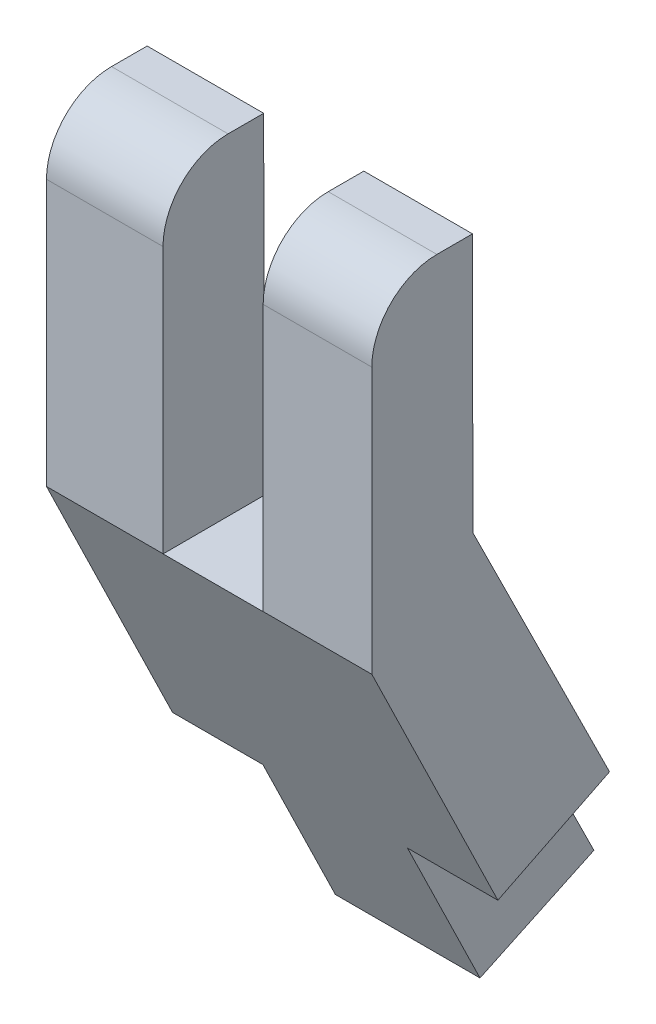
SolidWorks part; units mm, degrees
ref_plane "Front Plane" through (0, 0, 0) normal (0, 0, 1) x (1, 0, 0)
ref_plane "Top Plane" through (0, 0, 0) normal (0, 1, 0) x (1, 0, 0)
ref_plane "Right Plane" through (0, 0, 0) normal (1, 0, 0) x (0, 0, -1)
sketch "Sketch1" plane through (0, 0, 0) normal (0, 0, 1) x (1, 0, 0)
  line L0 (-2.5151, 0) -> (7.5105, 0) construction
  line L1 (2.4977, 0) -> (2.4977, 5.0158) construction
  line L3 (2.4977, 4.6362) -> (2.4977, 5.0158)
  line L5 (-2.8151, 0.4082) -> (-2.4998, 0.4072)
  line L6 (-2.5151, -0.4082) -> (-2.8151, -0.4082)
  arc A2 (-2.8151, 0.4082) -> (-2.8151, -0.4082) centre (-2.8151, 0) ccw
  arc A5 (-2.1151, 0.0013) -> (-2.5151, -0.4082) centre (-2.5234, 0) cw
  arc A6 (-2.1151, 0.0013) -> (2.4977, 4.6362) centre (2.5819, -0.0604) cw
  arc A7 (-2.4998, 0.4072) -> (2.4977, 5.0158) centre (2.4848, 0.0158) cw
revolve "Revolve1" [suppressed] add sketch "Sketch1" angle 360 about L1
sketch "Sketch3" plane through (0, 0, 0) normal (1, 0, 0) x (0, 0, -1)
  line L0 (-5.1915, 13.2582) -> (-5.1862, 9.6741)
  line L1 (-2.2625, 3.7845) -> (-3.8381, 3.0429)
  line L6 (-6.5841, 8.6789) -> (-6.5841, 13.2582)
  line L7 (-6.5841, 13.2582) -> (-5.1915, 13.2582)
  line L12 (-2.2625, 3.7845) -> (-5.1862, 9.6741)
  line L13 (-3.8381, 3.0429) -> (-6.5841, 8.6789)
extrude "Boss-Extrude1" add sketch "Sketch3" along normal blind 4.5 separate body
sketch "Sketch4" plane through (0, -0.0108, 5.1659) normal (0, 0.0021, -1) x (-1, 0, 0)
  line L0 (-2.997, 8.6897) -> (-2.997, 13.2897)
  line L1 (-2.997, 8.6897) -> (-1.6118, 8.6897)
  line L2 (-1.6118, 8.6897) -> (-1.6118, 13.2897)
  line L3 (-2.997, 13.2897) -> (-1.6118, 13.2897)
extrude "Cut-Extrude1" cut sketch "Sketch4" against normal up to next and the other way blind 4.5
sketch "Sketch5" plane through (0, 0, 0) normal (0, 0, 1) x (1, 0, 0)
  line L0 (-0.8483, 3.3998) -> (-0.8483, 3.73)
  line L1 (-4.3349, 3.3998) -> (-4.5715, 3.5649)
  line L2 (-4.0983, 3.3998) -> (-4.3349, 3.3998)
  line L3 (-4.5715, 3.5649) -> (-4.5715, 3.73)
  line L4 (-4.5715, 3.73) -> (-0.8483, 3.73)
  line L5 (-2.7483, 3.3998) -> (-0.8483, 3.3998)
  line L6 (-2.7483, 3.3998) -> (-2.7483, 2.9514)
  line L7 (-2.7483, 2.9514) -> (-4.0983, 3.3998)
  line L9 (-2.1455, 4.33) -> (-4.3035, 4.33) construction
revolve "Revolve2" [suppressed] add sketch "Sketch5" angle 360 about L9
sketch "Sketch6" [suppressed] plane through (-3.9715, 0, 0) normal (-1, 0, 0) x (0, 0, 1)
  circle A0 centre (0, 4.33) radius 0.6
extrude "Cut-Extrude2" [suppressed] cut sketch "Sketch6" against normal blind 6
sketch "Sketch7" [suppressed] plane through (-0.8483, 0, 0) normal (1, 0, 0) x (0, 0, -1)
  arc A2 (0.668, 3.6826) -> (-0.668, 3.6826) centre (0, 4.33) ccw construction
  circle A4 centre (0, 4.33) radius 0.9302
  circle A5 centre (0, 4.33) radius 0.6
extrude "Boss-Extrude2" [suppressed] add sketch "Sketch7" along normal blind 4
sketch "Sketch8" [suppressed] plane through (0, 0, 0) normal (0, 0, 1) x (1, 0, 0)
  line L0 (7.1105, 0.0013) -> (2.4977, 0.0013)
  line L1 (7.1105, 0.0013) -> (-2.1151, 0.0013) construction
  line L2 (2.4977, 0.0013) -> (2.4977, 4.5956)
  arc A0 (7.1105, 0.0013) -> (2.4977, 4.5956) centre (2.5366, 0.0217) ccw
  spline S0 degree 3 poles (3.1517, 4.5407) (2.9658, 4.5712) (2.7792, 4.5898) (2.404, 4.5991) (2.2144, 4.5893) (2.0285, 4.567) knots 0 0 0 0 0.5 0.5 1 1 1 1 construction
revolve "Cut-Revolve1" [suppressed] cut sketch "Sketch8" angle 360 about L2
fillet "Fillet1" radius 0.9 2 edges at (0.8059, 13.2582, 6.5841) (3.7485, 13.2582, 6.5841)
sketch "Sketch9" plane through (0, -0.1529, 0.308) normal (0, 0.4446, -0.8957) x (-1, 0, 0)
  line L0 (-2.25, 4.3959) -> (-2.25, 7.3959) construction
  line L1 (-4.5, 4.3959) -> (0, 4.3959) construction
  line L2 (0, 6.7208) -> (0, 4.3959)
  line L3 (-1.25, 6.7208) -> (-1.25, 4.3959)
  line L4 (-3.25, 6.7208) -> (-3.25, 4.3959)
  line L5 (0, 4.3959) -> (0, 10.9711) construction
  line L6 (-4.5, 6.7208) -> (-4.5, 4.3959)
  line L7 (0, 4.3959) -> (-1.25, 4.3959)
  line L8 (-3.25, 4.3959) -> (-4.5, 4.3959)
  line L13 (-3.25, 6.7208) -> (-4.5, 6.7208)
  line L14 (-1.25, 6.7208) -> (0, 6.7208)
extrude "Cut-Extrude3" cut sketch "Sketch9" against normal up to next
